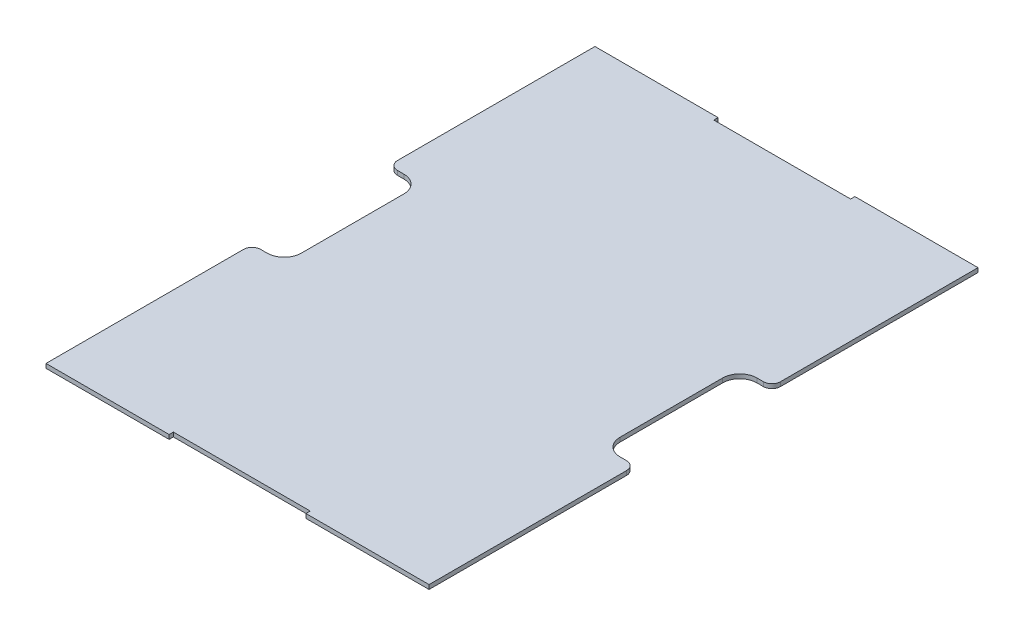
SolidWorks part; units mm, degrees
ref_plane "Front Plane" through (0, 0, 0) normal (0, 0, 1) x (1, 0, 0)
ref_plane "Top Plane" through (0, 0, 0) normal (0, 1, 0) x (1, 0, 0)
ref_plane "Right Plane" through (0, 0, 0) normal (1, 0, 0) x (0, 0, -1)
sketch "Sketch1" plane through (0, 0, 0) normal (0, 1, 0) x (1, 0, 0)
  line L0 (0, 112.8818) -> (0, 66.1241) construction
  line L1 (-71.12, 101.9175) -> (-25.4, 101.9175)
  line L2 (-71.12, 101.9175) -> (-71.12, 25.4)
  line L3 (-71.12, -101.9175) -> (-25.4, -101.9175)
  line L4 (71.12, 101.9175) -> (71.12, 25.4)
  line L6 (-25.4, 101.9175) -> (-25.4, 100.33)
  line L7 (-25.4, 100.33) -> (25.4, 100.33)
  line L8 (25.4, 101.9175) -> (25.4, 100.33)
  line L10 (-25.4, -101.9175) -> (-25.4, -100.33)
  line L11 (-25.4, -100.33) -> (25.4, -100.33)
  line L12 (25.4, -101.9175) -> (25.4, -100.33)
  line L13 (25.4, 101.9175) -> (71.12, 101.9175)
  line L14 (25.4, -101.9175) -> (71.12, -101.9175)
  line L15 (-71.12, -25.4) -> (-71.12, -101.9175)
  line L16 (-71.12, -25.4) -> (-59.182, -25.4)
  line L18 (-71.12, 25.4) -> (-59.182, 25.4)
  line L19 (-59.182, -25.4) -> (-59.182, 25.4)
  line L20 (71.12, -25.4) -> (59.182, -25.4)
  line L22 (71.12, 25.4) -> (59.182, 25.4)
  line L23 (59.182, -25.4) -> (59.182, 25.4)
  line L24 (71.12, -25.4) -> (71.12, -101.9175)
  line L25 (-87.7544, 0) -> (-47.3436, 0) construction
  point P15 (0, -100.33)
  point P17 (0, 100.33)
  point P26 (59.182, 0)
  point P27 (-59.182, 0)
  dimension "D1" = 142.24
  dimension "D2" = 203.835
  dimension "D3" = 1.5875
  dimension "D4" = 1.5875
  dimension "D5" = 50.8
  dimension "D6" = 50.8
  dimension "D7" = 11.938
  dimension "D8" = 11.938
  dimension "D9" = 50.8
  dimension "D10" = 50.8
extrude "Boss-Extrude1" add sketch "Sketch1" along normal mid plane 1.5875
fillet "Fillet2" radius 6.35 4 edges at (59.182, 0, 25.4) (59.182, 0, -25.4) (-59.182, 0, 25.4) (-59.182, 0, -25.4)
fillet "Fillet3" radius 3.175 4 edges at (71.12, 0, 25.4) (71.12, 0, -25.4) (-71.12, 0, 25.4) (-71.12, 0, -25.4)
